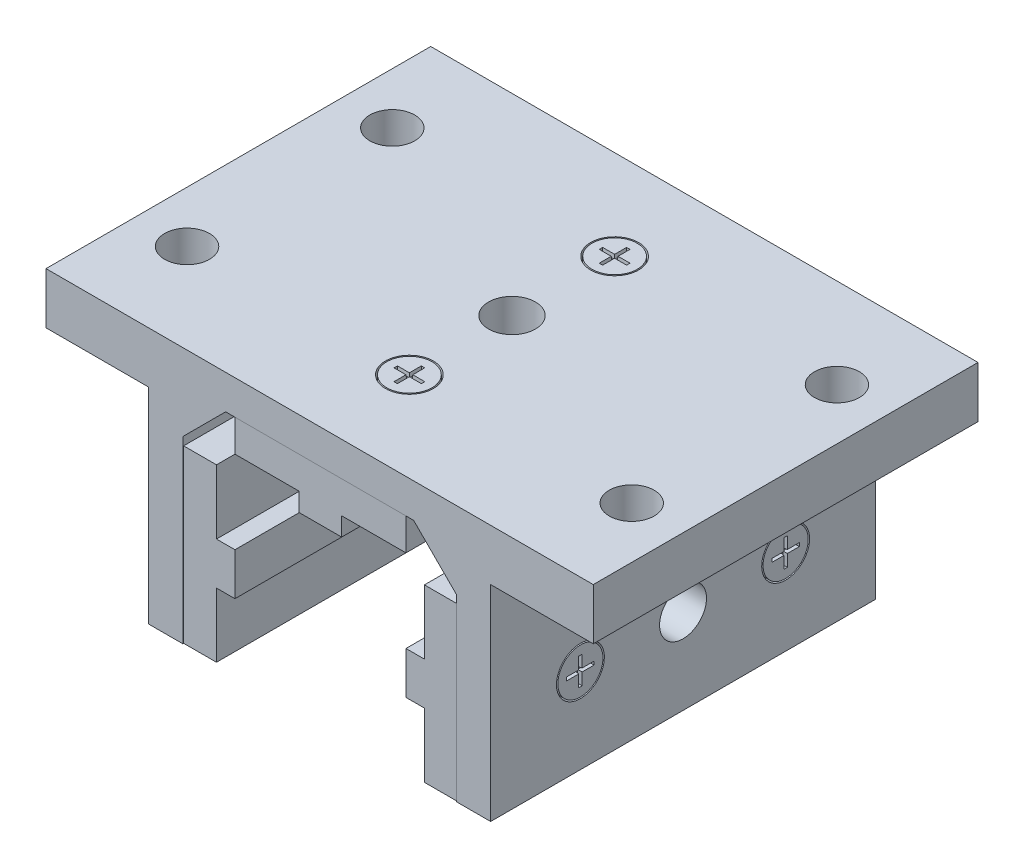
SolidWorks part; units mm, degrees
ref_plane "Front" through (0, 0, 0) normal (0, 0, 1) x (1, 0, 0)
ref_plane "Top" through (0, 0, 0) normal (0, 1, 0) x (1, 0, 0)
ref_plane "Right" through (0, 0, 0) normal (1, 0, 0) x (0, 0, -1)
sketch "Sketch1" plane through (0, 0, 0) normal (0, 0, 1) x (1, 0, 0)
  line L0 (-25.4, 0) -> (-25.4, 33.3248)
  line L1 (-31.75, 47.625) -> (31.75, 47.625)
  line L2 (-31.75, 47.625) -> (-31.75, 0)
  line L3 (-31.75, 0) -> (-25.4, 0)
  line L4 (31.75, 47.625) -> (31.75, 0)
  line L5 (-25.4, 33.3248) -> (-17.4498, 41.275)
  line L6 (-17.4498, 41.275) -> (17.4498, 41.275)
  line L7 (17.4498, 41.275) -> (25.4, 33.3248)
  line L8 (25.4, 33.3248) -> (25.4, 0)
  line L9 (25.4, 0) -> (31.75, 0)
  line L11 (-25.4, 0) -> (25.4, 0) construction
  dimension "Oall Ht" = 47.625
  dimension "Base Wd" = 63.5
  dimension "D2" = 45
  dimension "Leg Thick" = 6.35
  dimension "Top Thick" = 6.35
  dimension "Peak Wd" = 34.8996
extrude "Boss-Extrude1" add sketch "Sketch1" along normal mid plane 71.4248
sketch "Sketch2" plane through (0, 0, 0) normal (0, 0, 1) x (1, 0, 0)
  line L0 (-19.304, 19.812) -> (-19.304, 31.75)
  line L1 (-25.4, 0) -> (-19.304, 0)
  line L2 (-25.4, 0) -> (-25.4, 31.75)
  line L3 (-25.4, 31.75) -> (-19.304, 31.75)
  line L4 (-19.304, 0) -> (-19.304, 11.938)
  line L5 (-19.304, 19.812) -> (-15.875, 19.812)
  line L7 (-19.304, 11.938) -> (-15.875, 11.938)
  line L8 (-15.875, 19.812) -> (-15.875, 11.938)
  line L12 (-17.4498, 41.275) -> (17.4498, 41.275) construction
  line L13 (-15.875, 41.275) -> (15.875, 41.275)
  line L14 (-15.875, 41.275) -> (-15.875, 35.179)
  line L15 (-15.875, 35.179) -> (-3.937, 35.179)
  line L16 (15.875, 41.275) -> (15.875, 35.179)
  line L17 (3.937, 35.179) -> (15.875, 35.179)
  line L19 (-3.937, 35.179) -> (-3.937, 31.75)
  line L20 (-3.937, 31.75) -> (3.937, 31.75)
  line L21 (3.937, 35.179) -> (3.937, 31.75)
  point P14 (-15.875, 15.875)
  point P28 (0, 41.275)
  dimension "Pad Wd" = 31.75
  dimension "Pad Thick 1" = 9.525
  dimension "Pad Thick 2" = 6.096
  dimension "Pad Nose" = 7.874
extrude "Boss-Extrude2" add sketch "Sketch2" along normal mid plane 71.12 separate body
sketch "Sketch11" plane through (-15.875, 0, 0) normal (1, 0, 0) x (0, 0, -1)
  line L0 (-35.56, 19.812) -> (35.56, 19.812) construction
  line L1 (-3.937, 19.812) -> (3.937, 19.812)
  line L2 (-3.937, 19.812) -> (-3.937, 11.938)
  line L3 (-3.937, 11.938) -> (3.937, 11.938)
  line L4 (3.937, 19.812) -> (3.937, 11.938)
  line L5 (-35.56, 11.938) -> (35.56, 11.938) construction
  point P8 (0, 19.812)
extrude "Cut-Extrude5" cut sketch "Sketch11" against normal through all
sketch "Sketch12" plane through (0, 31.75, 0) normal (0, -1, 0) x (1, 0, 0)
  line L0 (-3.937, 35.56) -> (-3.937, -35.56) construction
  line L1 (-3.937, 3.937) -> (3.937, 3.937)
  line L2 (-3.937, 3.937) -> (-3.937, -3.937)
  line L3 (-3.937, -3.937) -> (3.937, -3.937)
  line L4 (3.937, 3.937) -> (3.937, -3.937)
  line L5 (3.937, 35.56) -> (3.937, -35.56) construction
  point P8 (-3.937, 0)
extrude "Cut-Extrude6" cut sketch "Sketch12" against normal through all
mirror "Mirror1" about plane through (0, 0, 0) normal (1, 0, 0) of bodies 126 109
sketch "Sketch3" plane through (0, 47.625, 0) normal (0, 1, 0) x (1, 0, 0)
  line L0 (0, -19.05) -> (0, 19.05) construction
  circle A0 centre (0, -19.05) radius 4.445
  circle A1 centre (0, -19.05) radius 4.191
  dimension "D1" = 0.254
  dimension "Screw Head Dia" = 8.89
  dimension "Screw Spacing" = 38.1
extrude "Cut-Extrude1" cut sketch "Sketch3" against normal blind 3.175
sketch "Sketch5" plane through (0, 47.625, 0) normal (0, 1, 0) x (1, 0, 0)
  line L0 (0.3175, -18.7325) -> (2.54, -18.7325)
  line L1 (-0.3175, -16.51) -> (0.3175, -16.51)
  line L2 (-0.3175, -16.51) -> (-0.3175, -18.7325)
  line L3 (-0.3175, -21.59) -> (0.3175, -21.59)
  line L4 (0.3175, -16.51) -> (0.3175, -18.7325)
  line L5 (-2.54, -18.7325) -> (-0.3175, -18.7325)
  line L6 (-2.54, -18.7325) -> (-2.54, -19.3675)
  line L7 (-2.54, -19.3675) -> (-0.3175, -19.3675)
  line L8 (2.54, -18.7325) -> (2.54, -19.3675)
  line L9 (-0.3175, -19.3675) -> (-0.3175, -21.59)
  line L10 (0.3175, -19.3675) -> (0.3175, -21.59)
  line L11 (0.3175, -19.3675) -> (2.54, -19.3675)
  line L12 (-0.3175, -18.7325) -> (0.3175, -19.3675) construction
  dimension "D1" = 0.635
  dimension "D2" = 5.08
extrude "Cut-Extrude2" cut sketch "Sketch5" against normal blind 0.762 draft 5
sketch "Sketch13" plane through (31.75, 0, 0) normal (1, 0, 0) x (0, 0, -1)
  circle A0 centre (-19.05, 15.875) radius 4.445
  dimension "D1" = 8.89
extrude "Cut-Extrude-Thin1" cut sketch "Sketch13" against normal blind 3.175 thin thin type one direction reverse wall 0.254
sketch "Sketch14" plane through (31.75, 0, 0) normal (1, 0, 0) x (0, 0, -1)
  line L0 (-19.3675, 15.5575) -> (-19.3675, 13.335)
  line L1 (-19.3675, 18.415) -> (-18.7325, 18.415)
  line L2 (-19.3675, 18.415) -> (-19.3675, 16.1925)
  line L3 (-19.3675, 13.335) -> (-18.7325, 13.335)
  line L4 (-18.7325, 18.415) -> (-18.7325, 16.1925)
  line L5 (-21.59, 16.1925) -> (-19.3675, 16.1925)
  line L6 (-21.59, 16.1925) -> (-21.59, 15.5575)
  line L7 (-21.59, 15.5575) -> (-19.3675, 15.5575)
  line L8 (-16.51, 16.1925) -> (-16.51, 15.5575)
  line L9 (-18.7325, 16.1925) -> (-16.51, 16.1925)
  line L10 (-18.7325, 15.5575) -> (-18.7325, 13.335)
  line L11 (-18.7325, 15.5575) -> (-16.51, 15.5575)
  line L12 (-19.3675, 16.1925) -> (-18.7325, 15.5575) construction
  dimension "D1" = 0.635
  dimension "D2" = 5.08
extrude "Cut-Extrude7" cut sketch "Sketch14" against normal blind 0.762 draft 5
mirror "Mirror4" about plane through (0, 0, 0) normal (1, 0, 0) of "Cut-Extrude7", "Cut-Extrude-Thin1"
mirror "Mirror3" about plane through (0, 0, 0) normal (0, 0, 1) of "Mirror4", "Cut-Extrude-Thin1", "Cut-Extrude7", "Cut-Extrude1", "Cut-Extrude2"
sketch "Sketch9" plane through (0, 47.625, 0) normal (0, 1, 0) x (1, 0, 0)
  circle A0 centre (0, 0) radius 4.3561
  dimension "Top Hole Dia" = 8.7122
extrude "Cut-Extrude4" cut sketch "Sketch9" against normal through all
sketch "Sketch15" plane through (0, 0, 0) normal (1, 0, 0) x (0, 0, -1)
  circle A0 centre (0, 15.875) radius 4.3561
  dimension "Side Wall Hole Dia" = 8.7122
extrude "Cut-Extrude8" cut sketch "Sketch15" against normal through all and the other way through all
sketch "Sketch16" plane through (0, 0, 0) normal (0, 0, 1) x (1, 0, 0)
  line L1 (-50.8, 47.625) -> (-28.575, 47.625)
  line L2 (-50.8, 47.625) -> (-50.8, 38.1)
  line L3 (-50.8, 38.1) -> (-28.575, 38.1)
  line L4 (-28.575, 47.625) -> (-28.575, 38.1)
  line L5 (31.75, 47.625) -> (-31.75, 47.625) construction
  line L6 (28.575, 47.625) -> (50.8, 47.625)
  line L7 (28.575, 47.625) -> (28.575, 38.1)
  line L8 (28.575, 38.1) -> (50.8, 38.1)
  line L9 (50.8, 47.625) -> (50.8, 38.1)
  line L10 (-31.75, 0) -> (-25.4, 0) construction
  line L11 (25.4, 0) -> (31.75, 0) construction
  point P4 (-28.575, 0)
  point P13 (28.575, 0)
  dimension "Oall Wd" = 101.6
  dimension "Top Flange Thickness" = 9.525
extrude "Top Flange" add sketch "Sketch16" along normal up to surface and the other way up to surface
sketch "Sketch17" plane through (0, 47.625, 0) normal (0, 1, 0) x (1, 0, 0)
  line L0 (-41.275, 19.05) -> (41.275, -19.05) construction
  line L1 (-41.275, 19.05) -> (41.275, 19.05) construction
  line L2 (-41.275, 19.05) -> (-41.275, -19.05) construction
  line L3 (-41.275, -19.05) -> (41.275, -19.05) construction
  line L4 (41.275, 19.05) -> (41.275, -19.05) construction
  line L5 (-28.575, 19.05) -> (-31.75, 19.05) construction
  circle A0 centre (41.275, 19.05) radius 4.1656
  circle A1 centre (41.275, -19.05) radius 4.1656
  circle A2 centre (-41.275, 19.05) radius 4.1656
  circle A3 centre (-41.275, -19.05) radius 4.1656
  dimension "Top Flange Hole Dia" = 8.3312
  dimension "Top Flange Hole Spacing" = 82.55
extrude "Top Flange Hole" cut sketch "Sketch17" against normal through all
equation "\"D1@Cut-Extrude1\" = \"Top Thick@Sketch1\" * .5"
equation "\"D1@Sketch13\" = \"Screw Head Dia@Sketch3\""
equation "\"D1@Cut-Extrude-Thin1\" = \"Leg Thick@Sketch1\" * .5"
equation "\"D5@Cut-Extrude-Thin1\" = \"D1@Sketch3\""
equation "\"D1@Cut-Extrude7\" = \"D1@Cut-Extrude2\""
equation "\"D1@Sketch14\" = \"D1@Sketch5\""
equation "\"D2@Sketch14\" = \"D2@Sketch5\""
equation "\"D3@Cut-Extrude7\" = \"D3@Cut-Extrude2\""
